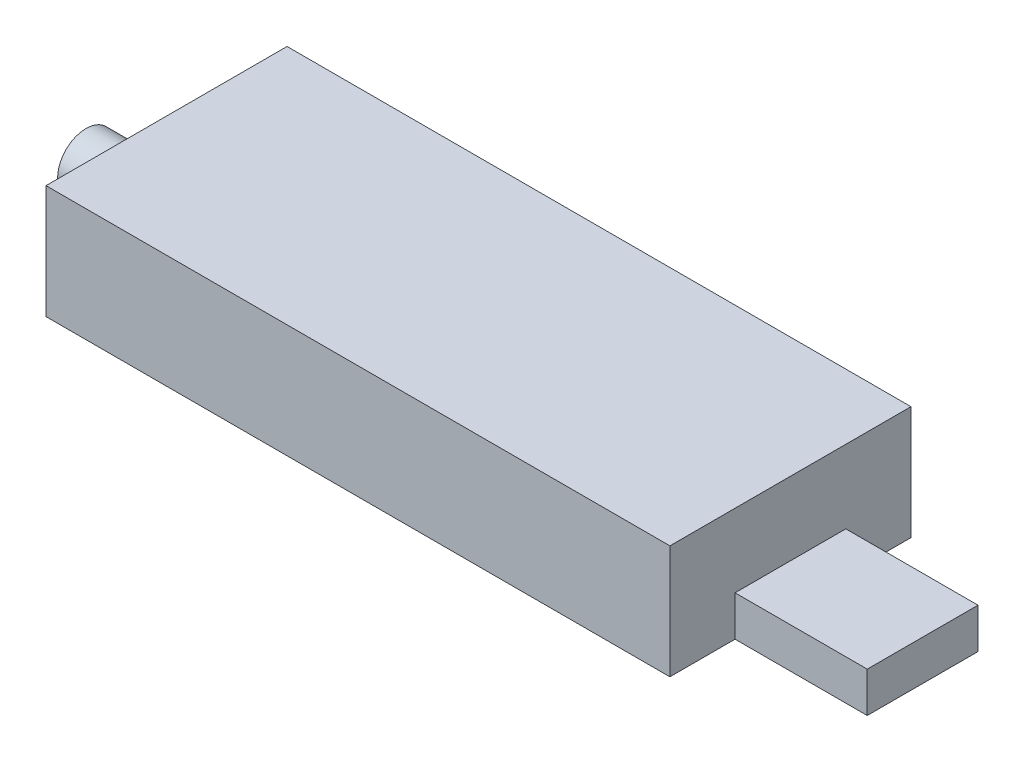
SolidWorks part; units mm, degrees
material "ABS"
ref_plane "Front Plane" through (0, 0, 0) normal (0, 0, 1) x (1, 0, 0)
ref_plane "Top Plane" through (0, 0, 0) normal (0, 1, 0) x (1, 0, 0)
ref_plane "Right Plane" through (0, 0, 0) normal (1, 0, 0) x (0, 0, -1)
sketch "Sketch1" plane through (0, 0, 0) normal (0, 1, 0) x (1, 0, 0)
  line L1 (0, 0) -> (69.85, 0)
  line L2 (0, 0) -> (0, 26.9875)
  line L3 (0, 26.9875) -> (69.85, 26.9875)
  line L4 (69.85, 0) -> (69.85, 26.9875)
  dimension "D1" = 69.85
  dimension "D2" = 26.9875
extrude "Boss-Extrude1" add sketch "Sketch1" along normal blind 12.7
sketch "Sketch2" plane through (69.85, 0, 0) normal (1, 0, 0) x (0, 0, -1)
  line L0 (0, 0) -> (26.9875, 0) construction
  line L1 (7.2937, 0) -> (19.6937, 0)
  line L2 (7.2937, 0) -> (7.2937, 4.5)
  line L3 (7.2937, 4.5) -> (19.6937, 4.5)
  line L4 (19.6937, 0) -> (19.6937, 4.5)
  point P6 (13.4937, 0)
  dimension "D1" = 12.4
  dimension "D2" = 4.5
extrude "Boss-Extrude2" add sketch "Sketch2" along normal blind 14.8
ref_plane "Plane1" through (-9.0125, 0, 0) normal (1, 0, 0) x (0, 0, -1)
sketch "Sketch3" plane through (0, 0, 0) normal (-1, 0, 0) x (0, 0, 1)
  line L0 (-26.9875, 0) -> (0, 0) construction
  line L1 (-13.4937, 3.81) -> (-13.4937, 0) construction
  circle A0 centre (-13.4937, 3.81) radius 3.175
  point P4 (-17.1135, 3.81)
  point P6 (-16.2804, 1.1135)
  point P7 (0, 0)
  dimension "D1" = 6.35
  dimension "D2" = 3.81
extrude "Boss-Extrude3" add sketch "Sketch3" along normal up to surface (9.0125 mm away) up to plane "Plane1"
